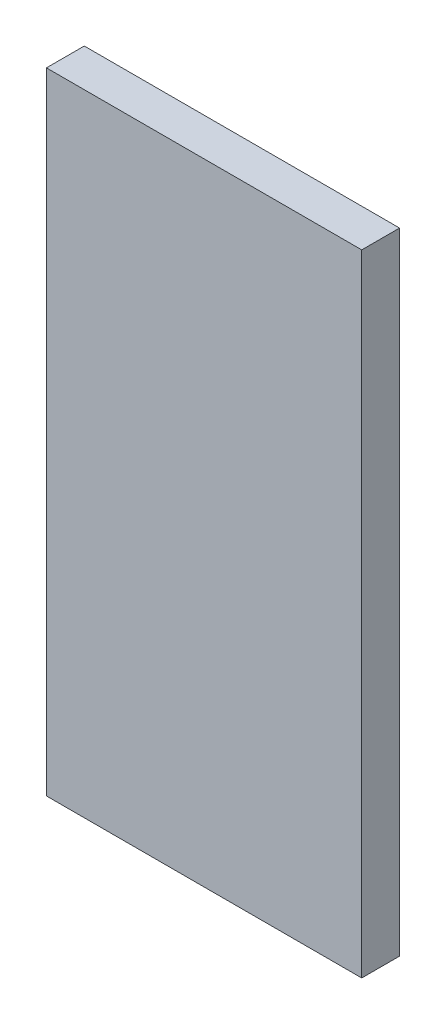
SolidWorks part; units mm, degrees
ref_plane "Alzado" through (0, 0, 0) normal (0, 0, 1) x (1, 0, 0)
ref_plane "Planta" through (0, 0, 0) normal (0, 1, 0) x (1, 0, 0)
ref_plane "Vista lateral" through (0, 0, 0) normal (1, 0, 0) x (0, 0, -1)
sketch "Croquis1" plane through (0, 0, 0) normal (0, 0, 1) x (1, 0, 0)
  line L1 (50, -100) -> (-50, -100)
  line L2 (50, -100) -> (50, 100)
  line L3 (50, 100) -> (-50, 100)
  line L4 (-50, -100) -> (-50, 100)
  line L5 (50, -100) -> (-50, 100) construction
  line L6 (50, 100) -> (-50, -100) construction
  point P0 (0, 0)
  dimension "D1" = 100
  dimension "D2" = 200
extrude "Saliente-Extruir1" add sketch "Croquis1" along normal blind 12
